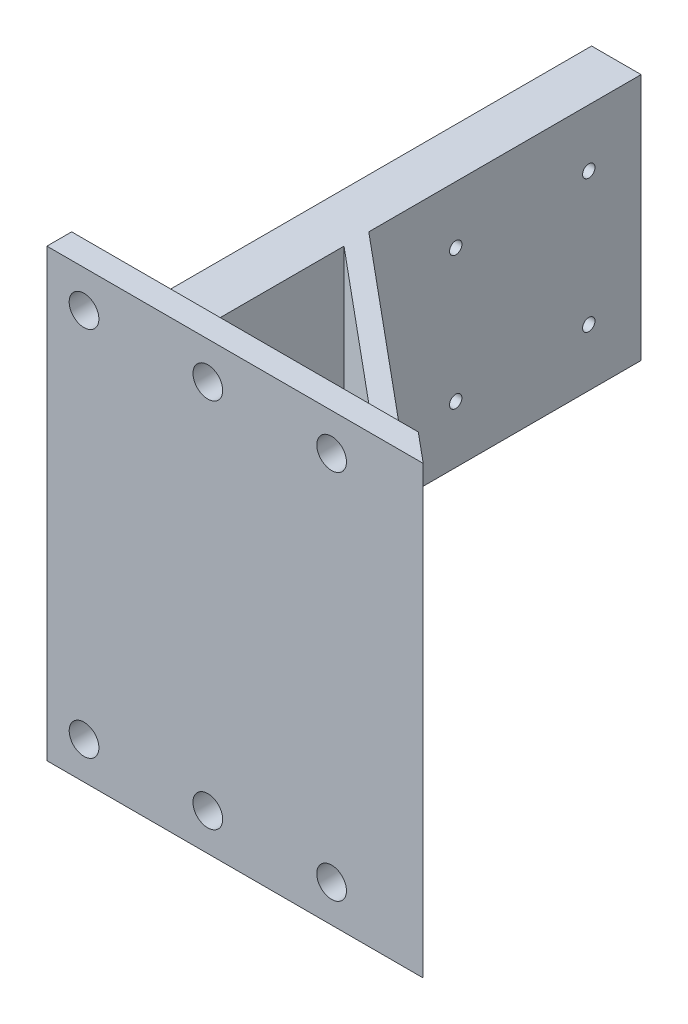
SolidWorks part; units mm, degrees
ref_plane "前视基准面" through (0, 0, 0) normal (0, 0, 1) x (1, 0, 0)
ref_plane "上视基准面" through (0, 0, 0) normal (0, 1, 0) x (1, 0, 0)
ref_plane "右视基准面" through (0, 0, 0) normal (1, 0, 0) x (0, 0, -1)
sketch "草图1" plane through (0, 0, 0) normal (0, 1, 0) x (1, 0, 0)
  line L0 (0, 0) -> (0, 110)
  line L1 (0, 110) -> (10, 110)
  line L2 (10, 110) -> (10, 55)
  line L3 (0, 0) -> (10, 0)
  line L4 (10, 0) -> (70, 0)
  line L5 (64, 5) -> (10, 50)
  line L6 (10, 50) -> (10, 5)
  line L7 (10, 55) -> (76, 0)
  line L8 (76, 0) -> (70, 0)
  line L9 (10, 5) -> (64, 5)
extrude "凸台-拉伸1" add sketch "草图1" along normal blind 50
sketch "草图2" plane through (0, 0, 0) normal (0, 0, 1) x (1, 0, 0)
  line L0 (0, 50) -> (0, 70)
  line L1 (0, 70) -> (76, 70)
  line L2 (76, 70) -> (76, 50)
  line L3 (76, 50) -> (76, 0) construction
  line L4 (0, 50) -> (76, 50) construction
  line L5 (76, 50) -> (0, 50)
extrude "凸台-拉伸2" add sketch "草图2" against normal blind 5
sketch "草图3" plane through (0, 50, 0) normal (0, -1, 0) x (1, 0, 0)
  line L0 (70, -5) -> (76, 0)
  line L1 (76, 0) -> (76, -5)
  line L2 (76, -5) -> (70, -5)
extrude "切除-拉伸1" cut sketch "草图3" against normal blind 44
sketch "草图4" plane through (0, 0, 0) normal (-1, 0, 0) x (0, 0, 1)
  line L0 (-110, 25) -> (0, 25) construction
  line L1 (-110, 50) -> (-110, 0) construction
  line L2 (0, 70) -> (0, 0) construction
ref_plane "基准面1" through (0, 25, 0) normal (0, -1, 0) x (0, 0, 1)
mirror "镜向1" about plane through (0, 25, 0) normal (0, -1, 0) of "切除-拉伸1", "凸台-拉伸2"
sketch "草图5" plane through (0, 0, 0) normal (-1, 0, 0) x (0, 0, 1)
  line L0 (0, 25) -> (-86, 25)
  line L1 (-110, 25) -> (0, 25) construction
  line L2 (-86, 25) -> (-72.565, 38.435) construction
  circle A0 centre (-86, 25) radius 19
  circle A1 centre (-72.565, 38.435) radius 1.25
  circle A2 centre (-72.565, 11.565) radius 1.25
  circle A3 centre (-99.435, 11.565) radius 1.25
  circle A4 centre (-99.435, 38.435) radius 1.25
  point P18 (-86, 25)
  dimension "D1" = 4
extrude "切除-拉伸2" cut sketch "草图5" against normal through all contours A4 | A1 | A3 | A2
sketch "草图6" plane through (0, 0, -5) normal (0, 0, -1) x (-1, 0, 0)
  line L0 (0, 25) -> (0, 62.5)
  line L1 (0, 50) -> (0, 0) construction
  line L2 (0, 70) -> (0, 50) construction
  line L3 (0, 62.5) -> (-7.5, 62.5)
  line L4 (-25, 62.5) -> (-32.5, 62.5)
  line L5 (-50, 62.5) -> (-57.5, 62.5)
  circle A0 centre (-7.5, 62.5) radius 3
  circle A1 centre (-32.5, 62.5) radius 3
  circle A2 centre (-57.5, 62.5) radius 3
  dimension "D1" = 3
extrude "切除-拉伸3" cut sketch "草图6" against normal through all
mirror "镜向2" about plane through (0, 25, 0) normal (0, -1, 0) of "切除-拉伸3"
